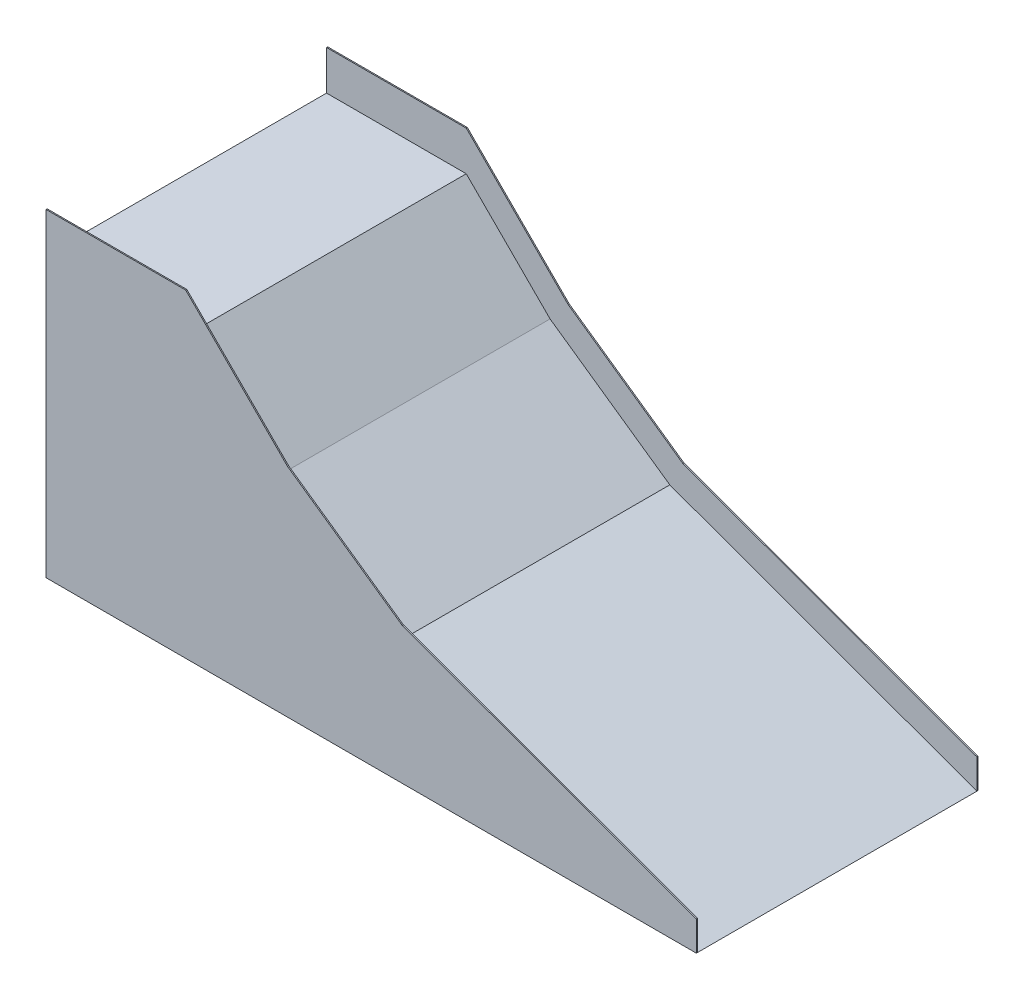
SolidWorks part; units mm, degrees
ref_plane "Ebene vorne" through (0, 0, 0) normal (0, 0, 1) x (1, 0, 0)
ref_plane "Ebene oben" through (0, 0, 0) normal (0, 1, 0) x (1, 0, 0)
ref_plane "Ebene rechts" through (0, 0, 0) normal (1, 0, 0) x (0, 0, -1)
sketch "Skizze1" plane through (0, 0, 0) normal (0, 0, 1) x (1, 0, 0)
  line L0 (0, 0) -> (0, 1000)
  line L1 (0, 1000) -> (500, 1000)
  line L2 (500, 1000) -> (800, 700)
  line L3 (800, 700) -> (1228.4444, 400)
  line L4 (1228.4444, 400) -> (2327.4354, 0)
  line L5 (2327.4354, 0) -> (0, 0)
  dimension "D1" = 1000
  dimension "D2" = 20
  dimension "D3" = 400
  dimension "D4" = 35
  dimension "D5" = 700
  dimension "D6" = 45
  dimension "D7" = 500
extrude "Aufsatz-Linear austragen1" add sketch "Skizze1" along normal mid plane 1000
sketch "Skizze3" plane through (0, 0, 500) normal (0, 0, 1) x (1, 0, 0)
  line L0 (0, 0) -> (0, 1141.4214)
  line L1 (0, 1141.4214) -> (500, 1141.4214)
  line L2 (500, 1141.4214) -> (864.5243, 776.8971)
  line L3 (864.5243, 776.8971) -> (1275.0177, 489.4665)
  line L4 (1275.0177, 489.4665) -> (2327.4354, 106.4178)
  line L5 (2327.4354, 106.4178) -> (2327.4354, 0)
  line L6 (0, 0) -> (2327.4354, 0) construction
  line L7 (800, 700) -> (500, 1000) construction
  line L8 (1228.4444, 400) -> (800, 700) construction
  line L9 (2327.4354, 0) -> (1228.4444, 400) construction
  line L10 (0, 0) -> (2327.4354, 0)
  dimension "D1" = 100
  dimension "D2" = 100
  dimension "D3" = 100
extrude "Aufsatz-Linear austragen2" add sketch "Skizze3" along normal blind 4
ref_plane "Ebene1" through (0, 0, 0) normal (0, 0, -1) x (-1, 0, 0)
mirror "Spiegeln1" about plane through (0, 0, 0) normal (0, 0, -1) of "Aufsatz-Linear austragen2"
